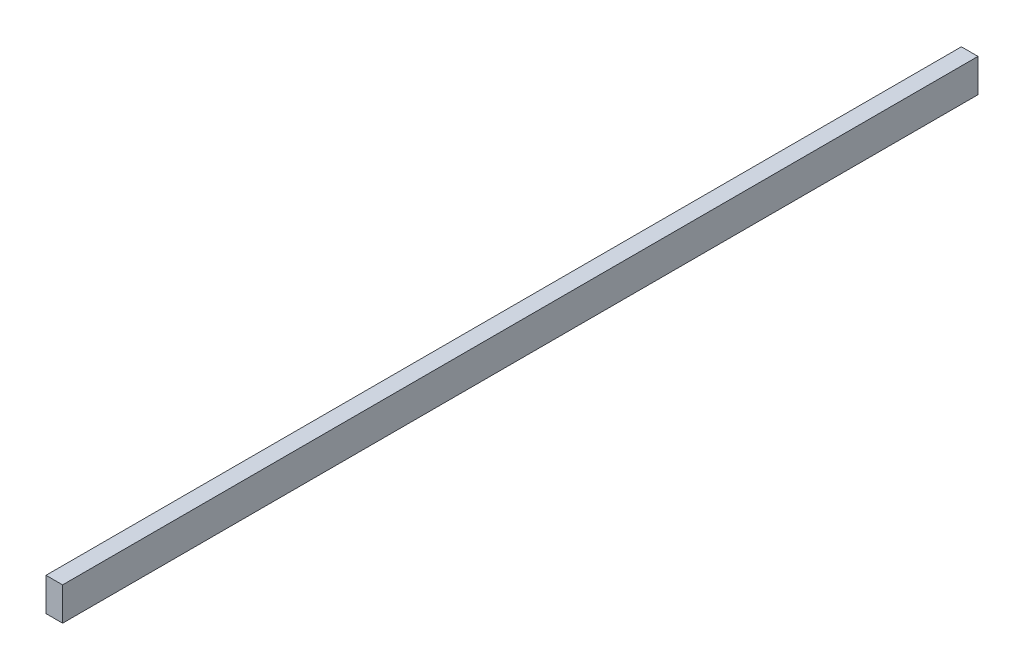
SolidWorks part; units mm, degrees
ref_plane "Alzado" through (0, 0, 0) normal (0, 0, 1) x (1, 0, 0)
ref_plane "Planta" through (0, 0, 0) normal (0, 1, 0) x (1, 0, 0)
ref_plane "Vista lateral" through (0, 0, 0) normal (1, 0, 0) x (0, 0, -1)
sketch "Croquis1" plane through (0, 0, 0) normal (0, 0, 1) x (1, 0, 0)
  line L1 (6.35, -12.7) -> (-6.35, -12.7)
  line L2 (6.35, -12.7) -> (6.35, 12.7)
  line L3 (6.35, 12.7) -> (-6.35, 12.7)
  line L4 (-6.35, -12.7) -> (-6.35, 12.7)
  line L5 (6.35, -12.7) -> (-6.35, 12.7) construction
  line L6 (6.35, 12.7) -> (-6.35, -12.7) construction
  point P0 (0, 0)
  dimension "D1" = 12.7
  dimension "D2" = 25.4
extrude "Saliente-Extruir1" add sketch "Croquis1" against normal blind 700
